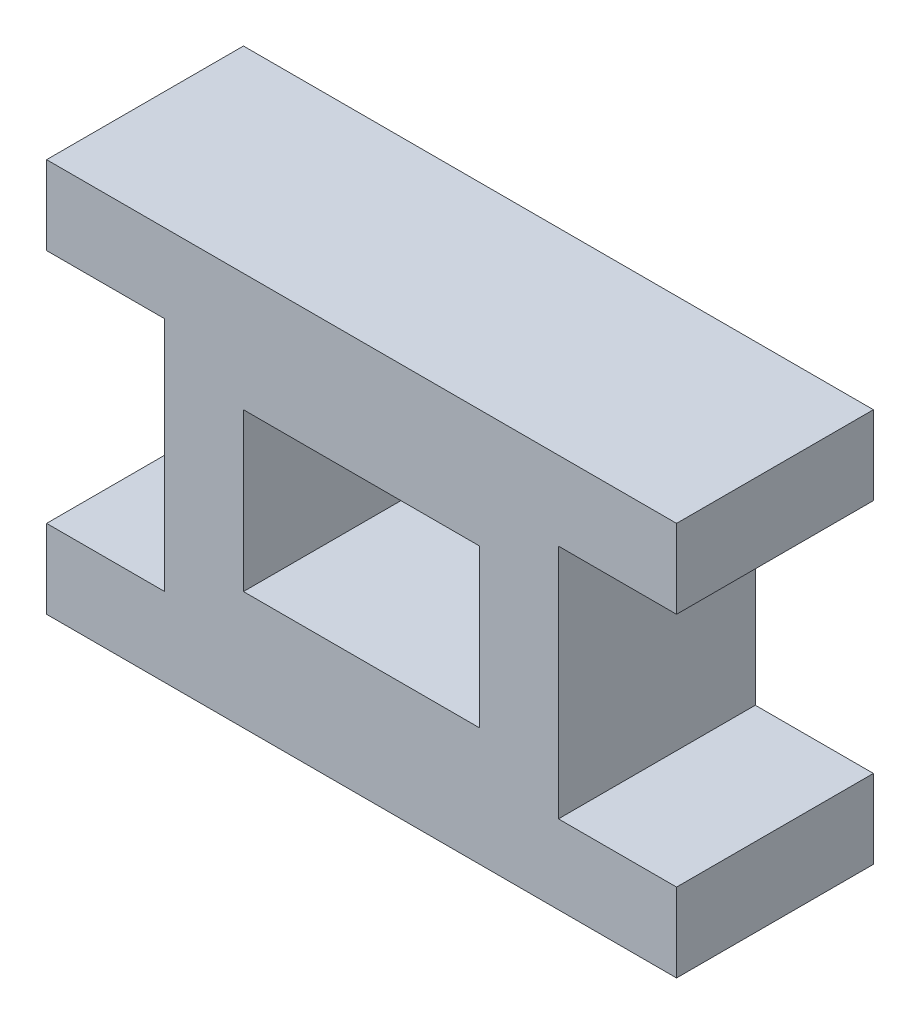
SolidWorks part; units mm, degrees
ref_plane "Front Plane" through (0, 0, 0) normal (0, 0, 1) x (1, 0, 0)
ref_plane "Top Plane" through (0, 0, 0) normal (0, 1, 0) x (1, 0, 0)
ref_plane "Right Plane" through (0, 0, 0) normal (1, 0, 0) x (0, 0, -1)
sketch "Sketch1" plane through (0, 0, 0) normal (0, 0, 1) x (1, 0, 0)
  line L0 (0, -3.2939) -> (0, -9.1582) construction
  line L1 (-40, -21.9369) -> (40, -21.9369)
  line L2 (40, -21.9369) -> (40, -11.9369)
  line L3 (40, -11.9369) -> (25, -11.9369)
  line L4 (25, -11.9369) -> (25, 18.0631)
  line L5 (25, 18.0631) -> (40, 18.0631)
  line L6 (40, 18.0631) -> (40, 28.0631)
  line L7 (40, 28.0631) -> (-40, 28.0631)
  line L8 (-15, 13.0631) -> (15, 13.0631)
  line L9 (15, 13.0631) -> (15, -6.9369)
  line L10 (15, -6.9369) -> (-15, -6.9369)
  line L11 (-15, 13.0631) -> (-15, -6.9369)
  line L12 (-40, 18.0631) -> (-40, 28.0631)
  line L13 (-25, 18.0631) -> (-40, 18.0631)
  line L14 (-25, -11.9369) -> (-25, 18.0631)
  line L15 (-40, -11.9369) -> (-25, -11.9369)
  line L16 (-40, -21.9369) -> (-40, -11.9369)
  point P2 (0, 0)
  point P16 (0, -6.9369)
  point P17 (0, 13.0631)
  point P18 (0, 28.0631)
  point P23 (0, -21.9369)
  dimension "D1" = 80
  dimension "D2" = 30
  dimension "D3" = 10
  dimension "D4" = 20
  dimension "D5" = 15
  dimension "D6" = 30
  dimension "D7" = 10
  dimension "D8" = 10
extrude "Boss-Extrude1" add sketch "Sketch1" along normal blind 25
